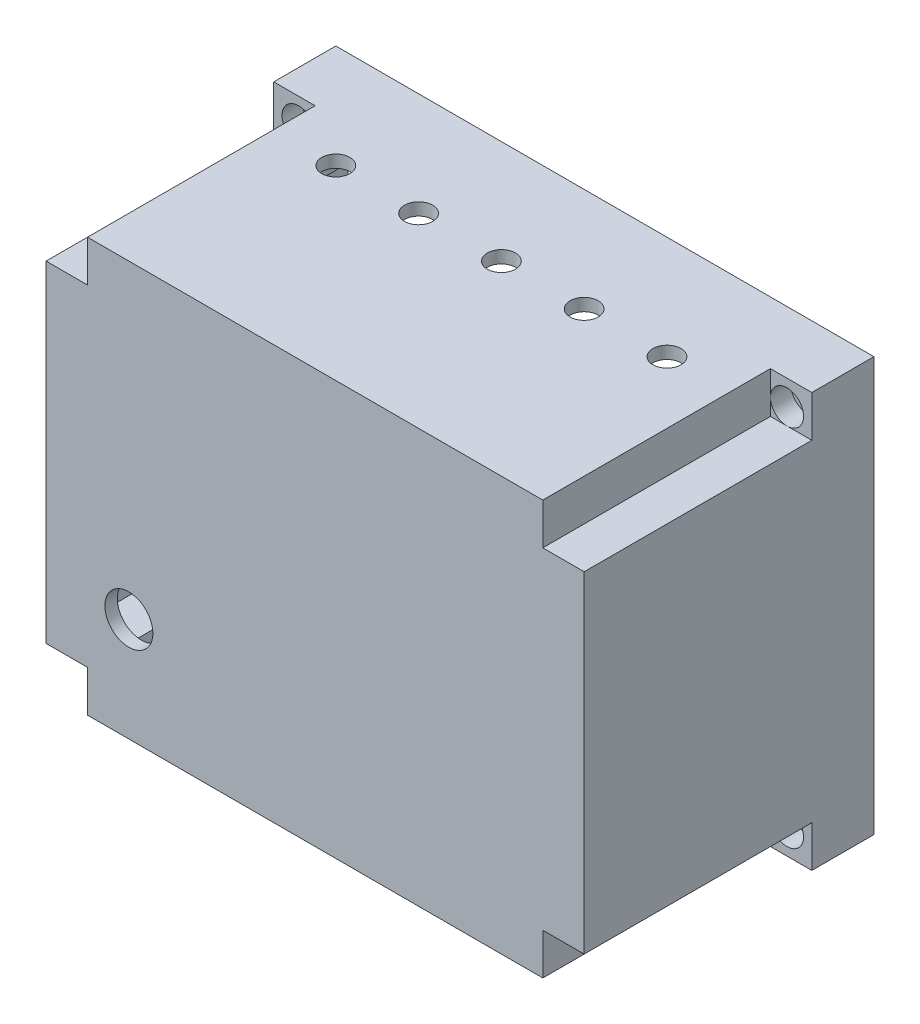
SolidWorks part; units mm, degrees
ref_plane "Front Plane" through (0, 0, 0) normal (0, 0, 1) x (1, 0, 0)
ref_plane "Top Plane" through (0, 0, 0) normal (0, 1, 0) x (1, 0, 0)
ref_plane "Right Plane" through (0, 0, 0) normal (1, 0, 0) x (0, 0, -1)
sketch "Sketch2" plane through (0, 0, 0) normal (0, 1, 0) x (1, 0, 0)
  line L1 (0, 0) -> (130, 0)
  line L2 (0, 0) -> (0, 70)
  line L3 (0, 70) -> (130, 70)
  line L4 (130, 0) -> (130, 70)
  dimension "D1" = 130
  dimension "D2" = 70
extrude "Boss-Extrude1" add sketch "Sketch2" along normal blind 100
sketch "Sketch3" plane through (0, 0, -70) normal (0, 0, -1) x (-1, 0, 0)
  line L0 (-130, 100) -> (0, 100) construction
  line L1 (-117, 87) -> (-13, 87)
  line L2 (-117, 87) -> (-117, 13)
  line L3 (-117, 13) -> (-13, 13)
  line L4 (-13, 87) -> (-13, 13)
  line L5 (-117, 87) -> (-13, 13) construction
  line L6 (-117, 13) -> (-13, 87) construction
  line L7 (-130, 100) -> (-130, 0) construction
  line L8 (-130, 0) -> (0, 0) construction
  line L9 (0, 100) -> (0, 0) construction
  point P0 (-65, 50)
  dimension "D1" = 13
  dimension "D2" = 13
  dimension "D3" = 13
  dimension "D4" = 13
extrude "Cut-Extrude1" cut sketch "Sketch3" against normal blind 67
sketch "Sketch4" plane through (0, 0, 0) normal (0, 0, 1) x (1, 0, 0)
  line L1 (0, 100) -> (10, 100)
  line L2 (0, 100) -> (0, 90)
  line L3 (0, 90) -> (10, 90)
  line L4 (10, 100) -> (10, 90)
  line L5 (130, 100) -> (120, 100)
  line L6 (130, 100) -> (130, 90)
  line L7 (130, 90) -> (120, 90)
  line L8 (120, 100) -> (120, 90)
  line L9 (0, 0) -> (10, 0)
  line L10 (0, 0) -> (0, 10)
  line L11 (0, 10) -> (10, 10)
  line L12 (10, 0) -> (10, 10)
  line L13 (130, 0) -> (120, 0)
  line L14 (130, 0) -> (130, 10)
  line L15 (130, 10) -> (120, 10)
  line L16 (120, 0) -> (120, 10)
  dimension "D1" = 10
  dimension "D2" = 10
  dimension "D3" = 10
  dimension "D4" = 10
  dimension "D5" = 10
  dimension "D6" = 10
  dimension "D7" = 10
  dimension "D8" = 10
extrude "Cut-Extrude2" cut sketch "Sketch4" against normal blind 55
sketch "Sketch5" plane through (0, 0, -70) normal (0, 0, -1) x (-1, 0, 0)
  line L0 (-130, 100) -> (0, 100) construction
  line L1 (-117, 87) -> (-13, 87)
  line L2 (-117, 87) -> (-117, 97)
  line L3 (-117, 97) -> (-13, 97)
  line L4 (-13, 87) -> (-13, 97)
  line L9 (-13, 13) -> (-117, 13)
  line L10 (-13, 13) -> (-13, 3)
  line L11 (-13, 3) -> (-117, 3)
  line L12 (-117, 13) -> (-117, 3)
  line L18 (-130, 0) -> (0, 0) construction
  dimension "D1" = 3
  dimension "D3" = 3
extrude "Cut-Extrude3" cut sketch "Sketch5" against normal blind 67
sketch "Sketch6" plane through (0, 0, -70) normal (0, 0, -1) x (-1, 0, 0)
  line L0 (-117, 97) -> (-117, 3) construction
  line L1 (-117, 87) -> (-127, 87)
  line L2 (-117, 87) -> (-117, 13)
  line L3 (-117, 13) -> (-127, 13)
  line L4 (-127, 87) -> (-127, 13)
  line L5 (-13, 3) -> (-13, 97) construction
  line L6 (-13, 87) -> (-3, 87)
  line L7 (-13, 87) -> (-13, 13)
  line L8 (-13, 13) -> (-3, 13)
  line L9 (-3, 87) -> (-3, 13)
  line L10 (-130, 100) -> (-130, 0) construction
  line L11 (-130, 100) -> (0, 100) construction
  line L12 (-130, 0) -> (0, 0) construction
  line L13 (0, 100) -> (0, 0) construction
  dimension "D1" = 3
  dimension "D2" = 13
  dimension "D3" = 13
  dimension "D4" = 13
  dimension "D5" = 3
  dimension "D6" = 13
extrude "Cut-Extrude4" cut sketch "Sketch6" against normal blind 67
sketch "Sketch9" plane through (0, 0, -70) normal (0, 0, -1) x (-1, 0, 0)
  line L0 (-130, 100) -> (0, 100) construction
  line L1 (-130, 100) -> (-130, 0) construction
  line L2 (0, 100) -> (0, 0) construction
  line L3 (-130, 0) -> (0, 0) construction
  circle A0 centre (-124, 94) radius 1.75
  circle A1 centre (-124, 6) radius 1.75
  circle A2 centre (-6, 94) radius 1.75
  circle A3 centre (-6, 6) radius 1.75
  dimension "D1" = 3.5
  dimension "D4" = 3.5
  dimension "D7" = 3.5
  dimension "D10" = 3.5
  dimension "D2" = 6
  dimension "D3" = 6
  dimension "D5" = 6
  dimension "D6" = 6
  dimension "D8" = 6
  dimension "D9" = 6
  dimension "D11" = 6
  dimension "D12" = 6
extrude "Cut-Extrude5" cut sketch "Sketch9" against normal blind 67
sketch "Sketch10" plane through (0, 0, -55) normal (0, 0, 1) x (1, 0, 0)
  line L0 (130, 100) -> (120, 100) construction
  line L1 (130, 90) -> (130, 100) construction
  circle A0 centre (124, 94) radius 4
  dimension "D3" = 8
  dimension "D1" = 6
  dimension "D2" = 6
extrude "Cut-Extrude6" cut sketch "Sketch10" against normal blind 5
sketch "Sketch12" plane through (0, 0, -55) normal (0, 0, 1) x (1, 0, 0)
  line L0 (130, 0) -> (130, 10) construction
  line L1 (120, 0) -> (130, 0) construction
  circle A0 centre (124, 6) radius 4
  dimension "D3" = 8
  dimension "D1" = 6
  dimension "D2" = 6
extrude "Cut-Extrude7" cut sketch "Sketch12" against normal blind 5
sketch "Sketch13" plane through (0, 0, -55) normal (0, 0, 1) x (1, 0, 0)
  line L0 (0, 0) -> (10, 0) construction
  line L1 (0, 10) -> (0, 0) construction
  circle A0 centre (6, 6) radius 4
  dimension "D3" = 8
  dimension "D1" = 6
  dimension "D2" = 6
extrude "Cut-Extrude8" cut sketch "Sketch13" against normal blind 5
sketch "Sketch14" plane through (0, 0, -55) normal (0, 0, 1) x (1, 0, 0)
  line L0 (0, 100) -> (0, 90) construction
  line L1 (10, 100) -> (0, 100) construction
  circle A0 centre (6, 94) radius 4
  dimension "D3" = 8
  dimension "D1" = 6
  dimension "D2" = 6
extrude "Cut-Extrude9" cut sketch "Sketch14" against normal blind 5
sketch "Sketch15" plane through (0, 0, -70) normal (0, 0, -1) x (-1, 0, 0)
  line L1 (-117, 87) -> (-120, 87)
  line L2 (-117, 87) -> (-117, 90)
  line L3 (-117, 90) -> (-120, 90)
  line L4 (-120, 87) -> (-120, 90)
  line L5 (-117, 13) -> (-120, 13)
  line L6 (-117, 13) -> (-117, 10)
  line L7 (-117, 10) -> (-120, 10)
  line L8 (-120, 13) -> (-120, 10)
  line L9 (-13, 13) -> (-10, 13)
  line L10 (-13, 13) -> (-13, 10)
  line L11 (-13, 10) -> (-10, 10)
  line L12 (-10, 13) -> (-10, 10)
  line L13 (-13, 87) -> (-10, 87)
  line L14 (-13, 87) -> (-13, 90)
  line L15 (-13, 90) -> (-10, 90)
  line L16 (-10, 87) -> (-10, 90)
  dimension "D1" = 3
  dimension "D2" = 3
  dimension "D3" = 3
  dimension "D4" = 3
  dimension "D5" = 3
  dimension "D6" = 3
  dimension "D7" = 3
  dimension "D8" = 3
extrude "Boss-Extrude2" add sketch "Sketch15" along normal blind 5
sketch "Sketch16" plane through (0, 3, 0) normal (0, 1, 0) x (1, 0, 0)
  line L3 (117, 70) -> (41, 70)
  line L4 (117, 70) -> (117, 67)
  line L5 (117, 67) -> (41, 67)
  line L6 (41, 70) -> (41, 67)
  dimension "D1" = 3
  dimension "D2" = 76
extrude "Boss-Extrude3" add sketch "Sketch16" along normal blind 15
sketch "Sketch17" plane through (0, 0, -3) normal (0, 0, -1) x (-1, 0, 0)
  line L0 (-117, 18) -> (-41, 18) construction
  line L1 (-101, 18) -> (-98, 18)
  line L2 (-101, 18) -> (-101, 48)
  line L3 (-101, 48) -> (-98, 48)
  line L4 (-98, 18) -> (-98, 48)
  line L5 (-117, 18) -> (-117, 13) construction
  line L6 (-38, 18) -> (-35, 18)
  line L7 (-38, 18) -> (-38, 48)
  line L8 (-38, 48) -> (-35, 48)
  line L9 (-35, 18) -> (-35, 48)
  dimension "D1" = 30
  dimension "D2" = 30
  dimension "D3" = 3
  dimension "D4" = 3
  dimension "D5" = 16
  dimension "D6" = 60
extrude "Boss-Extrude4" add sketch "Sketch17" along normal blind 15
sketch "Sketch18" plane through (0, 0, -3) normal (0, 0, -1) x (-1, 0, 0)
  line L0 (-130, 0) -> (0, 0) construction
  line L1 (0, 100) -> (0, 0) construction
  circle A0 centre (-20, 25) radius 5.8
  dimension "D1" = 11.6
  dimension "D2" = 25
  dimension "D3" = 20
extrude "Cut-Extrude10" cut sketch "Sketch18" against normal blind 15
sketch "Sketch19" plane through (0, 100, 0) normal (0, 1, 0) x (1, 0, 0)
  line L2 (0, 70) -> (0, 45) construction
  line L3 (0, 55) -> (0, 0) construction
  line L4 (0, 45) -> (130, 45) construction
  line L5 (130, 55) -> (130, 0) construction
  line L6 (10, 55) -> (10, 0) construction
  circle A0 centre (25, 45) radius 3.4
  circle A1 centre (45, 45) radius 3.4
  circle A2 centre (65, 45) radius 3.4
  circle A3 centre (85, 45) radius 3.4
  circle A4 centre (105, 45) radius 3.4
  dimension "D7" = 6.8
  dimension "D8" = 6.8
  dimension "D9" = 6.8
  dimension "D10" = 6.8
  dimension "D11" = 6.8
  dimension "D1" = 25
  dimension "D2" = 15
  dimension "D3" = 95
  dimension "D4" = 75
  dimension "D5" = 55
  dimension "D6" = 35
extrude "Cut-Extrude11" cut sketch "Sketch19" against normal blind 15
